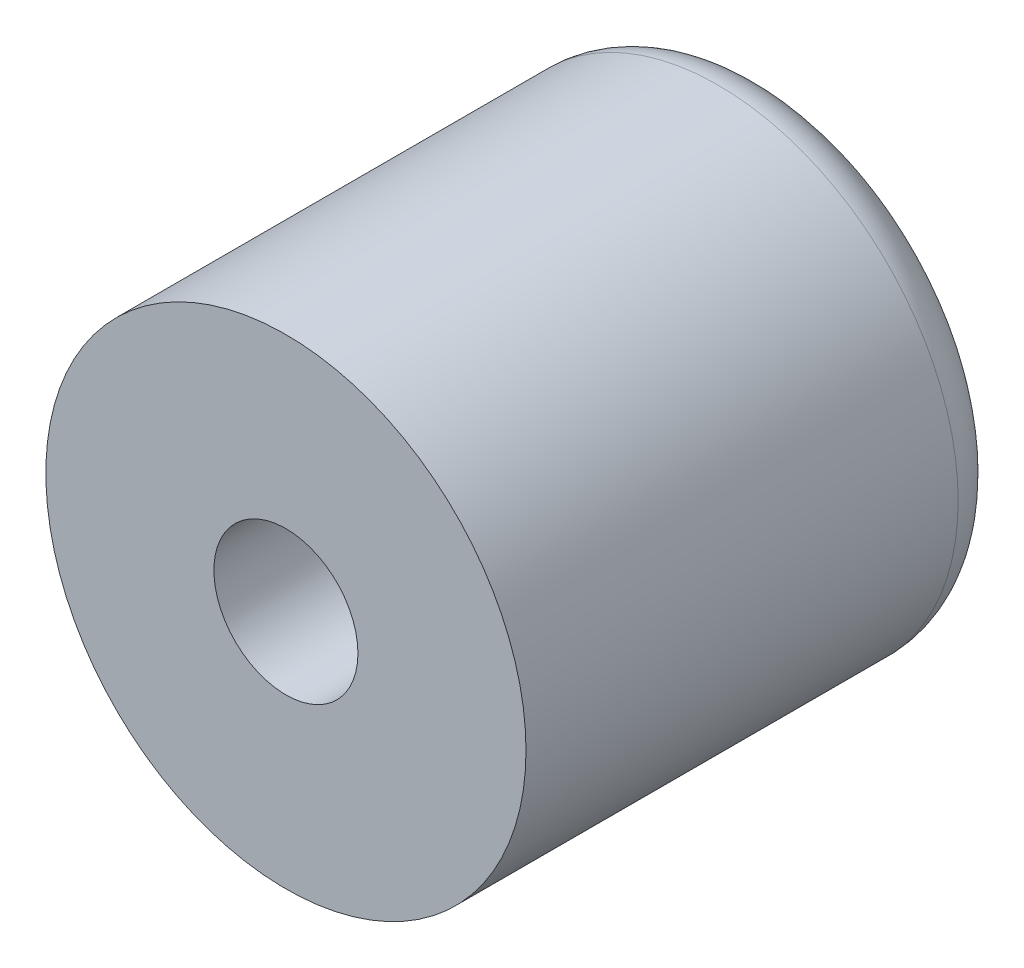
SolidWorks part; units mm, degrees
material "Plastique personnalisé"
ref_plane "Plan de face" through (0, 0, 0) normal (0, 0, 1) x (1, 0, 0)
ref_plane "Plan de dessus" through (0, 0, 0) normal (0, 1, 0) x (1, 0, 0)
ref_plane "Plan de droite" through (0, 0, 0) normal (1, 0, 0) x (0, 0, -1)
sketch "Esquisse1" plane through (0, 0, 0) normal (0, 0, 1) x (1, 0, 0)
  circle A0 centre (0, 0) radius 5
  dimension "D1" = 10
extrude "Boss.-Extru.1" add sketch "Esquisse1" along normal blind 10
sketch "Esquisse2" plane through (0, 0, 10) normal (0, 0, 1) x (1, 0, 0)
  circle A0 centre (0, 0) radius 1.5
extrude "Enlèv. mat.-Extru.1" cut sketch "Esquisse2" against normal blind 7
sketch "Esquisse3" plane through (0, 0, 3) normal (0, 0, 1) x (1, 0, 0)
  circle A0 centre (0, 0) radius 1
extrude "Enlèv. mat.-Extru.2" cut sketch "Esquisse3" against normal blind 7
fillet "Congé1" radius 1 1 edges at (5, 0, 0)
